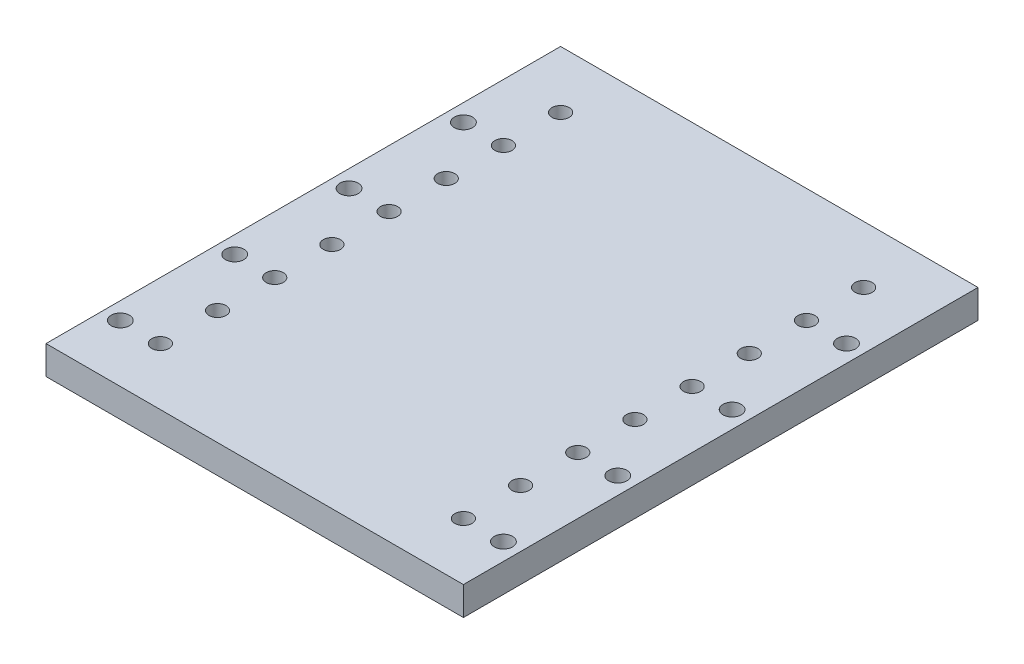
SolidWorks part; units mm, degrees
ref_plane "前视基准面" through (0, 0, 0) normal (0, 0, 1) x (1, 0, 0)
ref_plane "上视基准面" through (0, 0, 0) normal (0, 1, 0) x (1, 0, 0)
ref_plane "右视基准面" through (0, 0, 0) normal (1, 0, 0) x (0, 0, -1)
sketch "草图1" plane through (0, 0, 0) normal (0, 1, 0) x (1, 0, 0)
  line L1 (-36.5, -45) -> (36.5, -45)
  line L2 (-36.5, -45) -> (-36.5, 45)
  line L3 (-36.5, 45) -> (36.5, 45)
  line L4 (36.5, -45) -> (36.5, 45)
  line L5 (-36.5, -45) -> (36.5, 45) construction
  line L6 (-36.5, 45) -> (36.5, -45) construction
  point P0 (0, 0)
  dimension "D1" = 73
  dimension "D2" = 90
extrude "凸台-拉伸1" add sketch "草图1" along normal blind 5
sketch "草图2" plane through (0, 5, 0) normal (0, 1, 0) x (1, 0, 0)
  line L0 (-33.5, 45) -> (-33.5, -45) construction
  line L1 (36.5, 45) -> (-36.5, 45) construction
  line L2 (-36.5, -45) -> (36.5, -45) construction
  line L3 (0, 45) -> (0, -45) construction
  line L4 (-36.5, 45) -> (-36.5, -45) construction
  line L5 (-36.5, 25) -> (36.5, 25) construction
  line L6 (36.5, -45) -> (36.5, 45) construction
  line L7 (-36.5, 5) -> (36.5, 5) construction
  line L8 (-36.5, -15) -> (36.5, -15) construction
  line L9 (-36.5, -35) -> (36.5, -35) construction
  circle A0 centre (-33.5, 25) radius 1.6
  circle A1 centre (-33.5, 5) radius 1.6
  circle A2 centre (-33.5, -15) radius 1.6
  circle A3 centre (-33.5, -35) radius 1.6
  circle A4 centre (33.5, -35) radius 1.6
  circle A5 centre (33.5, -15) radius 1.6
  circle A6 centre (33.5, 5) radius 1.6
  circle A7 centre (33.5, 25) radius 1.6
  dimension "D6" = 3.2
  dimension "D1" = 3
  dimension "D2" = 20
  dimension "D3" = 20
  dimension "D4" = 40
  dimension "D5" = 60
extrude "切除-拉伸1" cut sketch "草图2" against normal through all
sketch "草图3" plane through (0, 5, 0) normal (0, 1, 0) x (1, 0, 0)
  line L0 (26.5, 45) -> (26.5, -45) construction
  line L1 (36.5, 45) -> (-36.5, 45) construction
  line L2 (-36.5, -45) -> (36.5, -45) construction
  line L3 (36.5, -45) -> (36.5, 45) construction
  line L4 (0, 45) -> (0, -45) construction
  circle A0 centre (26.5, 25) radius 1.5
  circle A1 centre (26.5, 15) radius 1.5
  circle A2 centre (26.5, 35) radius 1.5
  circle A7 centre (26.5, 5) radius 1.5
  circle A8 centre (26.5, -5) radius 1.5
  circle A9 centre (26.5, -15) radius 1.5
  circle A10 centre (26.5, -25) radius 1.5
  circle A11 centre (26.5, -35) radius 1.5
  circle A12 centre (-26.5, -35) radius 1.5
  circle A13 centre (-26.5, -25) radius 1.5
  circle A14 centre (-26.5, -15) radius 1.5
  circle A15 centre (-26.5, -5) radius 1.5
  circle A16 centre (-26.5, 5) radius 1.5
  circle A17 centre (-26.5, 15) radius 1.5
  circle A18 centre (-26.5, 25) radius 1.5
  circle A19 centre (-26.5, 35) radius 1.5
  dimension "D2" = 3
  dimension "D1" = 10
  dimension "D3" = 10
  dimension "D4" = 8
extrude "切除-拉伸2" cut sketch "草图3" against normal blind 10
